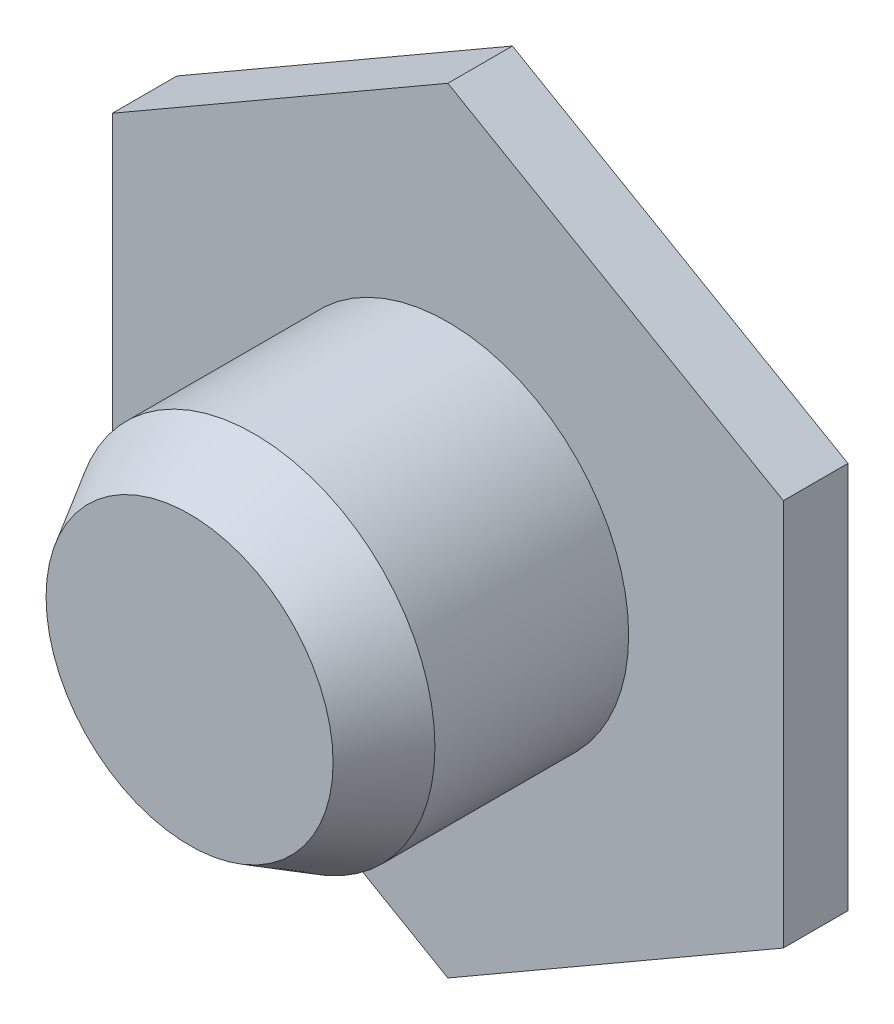
SolidWorks part; units mm, degrees
ref_plane "Front Plane" through (0, 0, 0) normal (0, 0, 1) x (1, 0, 0)
ref_plane "Top Plane" through (0, 0, 0) normal (0, 1, 0) x (1, 0, 0)
ref_plane "Right Plane" through (0, 0, 0) normal (1, 0, 0) x (0, 0, -1)
sketch "Sketch1" plane through (0, 0, 0) normal (0, 0, 1) x (1, 0, 0)
  line L1 (0, 3) -> (-2.5981, 1.5)
  line L2 (-2.5981, 1.5) -> (-2.5981, -1.5)
  line L3 (-2.5981, -1.5) -> (0, -3)
  line L4 (0, -3) -> (2.5981, -1.5)
  line L5 (2.5981, -1.5) -> (2.5981, 1.5)
  line L6 (2.5981, 1.5) -> (0, 3)
  circle A0 centre (0, 0) radius 2.5981 construction
extrude "Boss-Extrude1" add sketch "Sketch1" along normal blind 0.5
sketch "Sketch2" plane through (0, 0, 0.5) normal (0, 0, 1) x (1, 0, 0)
  circle A0 centre (0, 0) radius 1.4
extrude "Boss-Extrude2" add sketch "Sketch2" along normal blind 1.5 contours A0
sketch "Sketch3" plane through (0, 0, 2) normal (0, 0, 1) x (1, 0, 0)
  circle A0 centre (0, 0) radius 1.4
extrude "Boss-Extrude3" add sketch "Sketch3" along normal blind 0.5 draft 30
